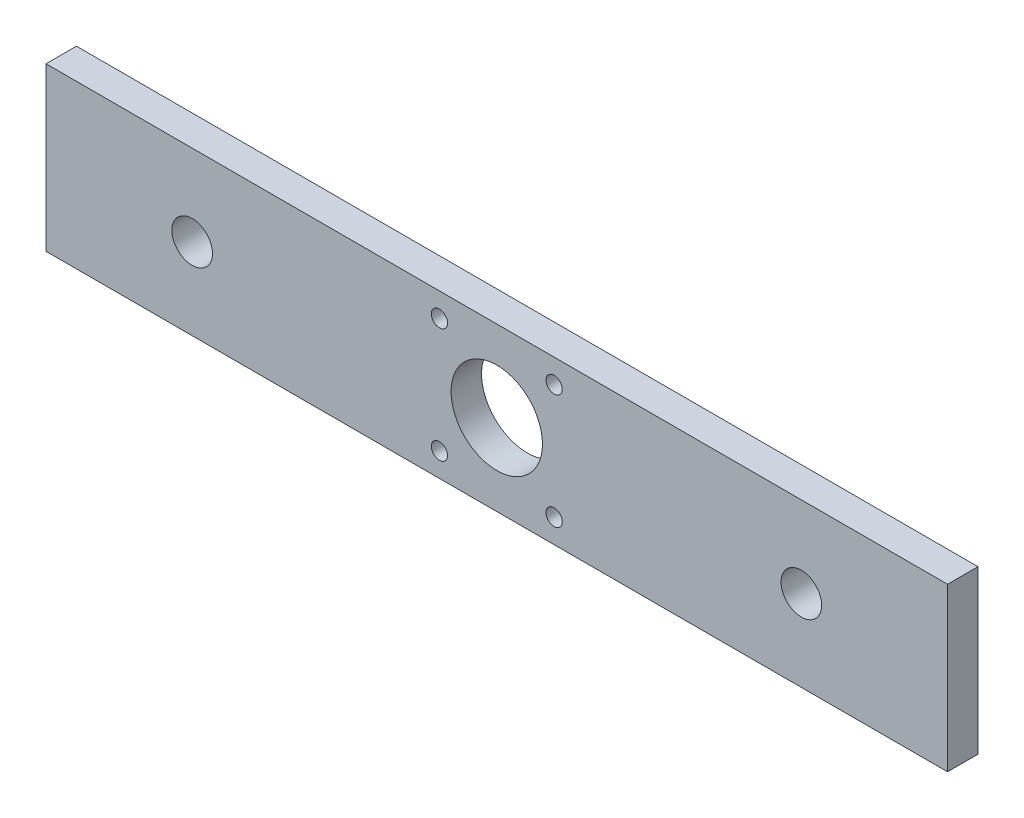
SolidWorks part; units mm, degrees
ref_plane "Alzado" through (0, 0, 0) normal (0, 0, 1) x (1, 0, 0)
ref_plane "Planta" through (0, 0, 0) normal (0, 1, 0) x (1, 0, 0)
ref_plane "Vista lateral" through (0, 0, 0) normal (1, 0, 0) x (0, 0, -1)
sketch "Croquis1" plane through (0, 0, 0) normal (0, 0, 1) x (1, 0, 0)
  line L0 (222, 0) -> (-222, 0) construction
  line L1 (-222, -40) -> (222, -40)
  line L2 (-222, -40) -> (-222, 40)
  line L3 (-222, 40) -> (222, 40)
  line L4 (222, -40) -> (222, 40)
  line L5 (-222, -40) -> (222, 40) construction
  line L6 (-222, 40) -> (222, -40) construction
  line L7 (-28.25, -28.25) -> (28.25, -28.25) construction
  line L8 (-28.25, -28.25) -> (-28.25, 28.25) construction
  line L9 (-28.25, 28.25) -> (28.25, 28.25) construction
  line L10 (28.25, -28.25) -> (28.25, 28.25) construction
  line L11 (-28.25, -28.25) -> (28.25, 28.25) construction
  line L12 (-28.25, 28.25) -> (28.25, -28.25) construction
  circle A0 centre (0, 0) radius 22.5
  circle A1 centre (28.25, 28.25) radius 4
  circle A2 centre (-28.25, 28.25) radius 4
  circle A3 centre (28.25, -28.25) radius 4
  circle A4 centre (-28.25, -28.25) radius 4
  circle A5 centre (-150, 0) radius 10
  circle A6 centre (150, 0) radius 10
  point P0 (0, 0)
  dimension "D3" = 45
  dimension "D6" = 8
  dimension "D7" = 20
  dimension "D8" = 20
  dimension "D1" = 80
  dimension "D2" = 444
  dimension "D4" = 56.5
  dimension "D5" = 56.5
  dimension "D9" = 300
  dimension "D10" = 72
extrude "Saliente-Extruir1" add sketch "Croquis1" against normal blind 15
